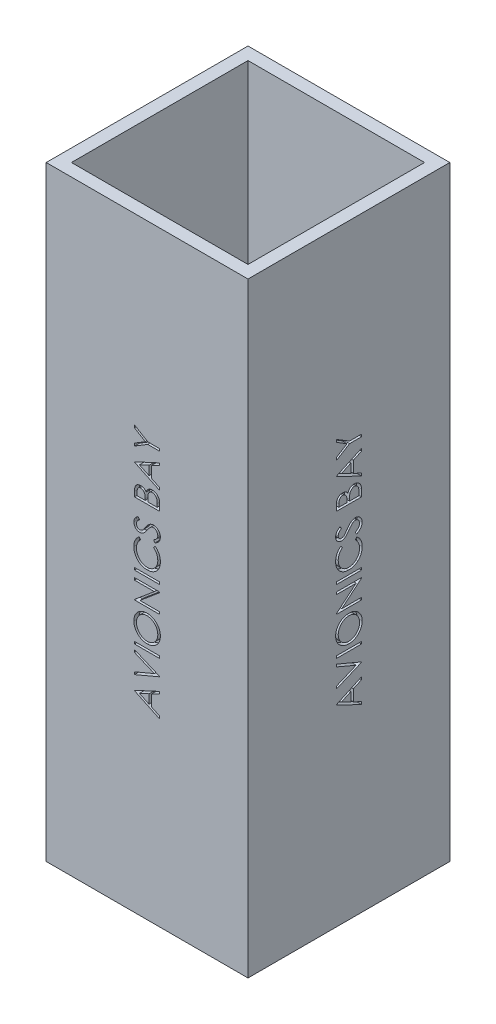
SolidWorks part; units mm, degrees
material "PVC Rigid"
ref_plane "Front Plane" through (0, 0, 0) normal (0, 0, 1) x (1, 0, 0)
ref_plane "Top Plane" through (0, 0, 0) normal (0, 1, 0) x (1, 0, 0)
ref_plane "Right Plane" through (0, 0, 0) normal (1, 0, 0) x (0, 0, -1)
sketch "Sketch1" plane through (0, 0, 0) normal (0, 1, 0) x (1, 0, 0)
  line L1 (-50.8, -50.8) -> (50.8, -50.8)
  line L2 (-50.8, -50.8) -> (-50.8, 50.8)
  line L3 (-50.8, 50.8) -> (50.8, 50.8)
  line L4 (50.8, -50.8) -> (50.8, 50.8)
  line L5 (-50.8, -50.8) -> (50.8, 50.8) construction
  line L6 (-50.8, 50.8) -> (50.8, -50.8) construction
  line L7 (-44.45, -44.45) -> (44.45, -44.45)
  line L8 (-44.45, -44.45) -> (-44.45, 44.45)
  line L9 (-44.45, 44.45) -> (44.45, 44.45)
  line L10 (44.45, -44.45) -> (44.45, 44.45)
  line L11 (-44.45, -44.45) -> (44.45, 44.45) construction
  line L12 (-44.45, 44.45) -> (44.45, -44.45) construction
  point P0 (0, 0)
  point P6 (0, 0)
  dimension "D1" = 101.6
  dimension "D2" = 101.6
  dimension "D3" = 88.9
extrude "Boss-Extrude1" add sketch "Sketch1" along normal blind 304.8
sketch "Sketch6" plane through (-50.8, 0, 0) normal (-1, 0, 0) x (0, 0, 1)
  line L0 (6.35, 0) -> (6.35, 304.8) construction
  line L1 (-50.8, 0) -> (50.8, 0) construction
  line L2 (-50.8, 304.8) -> (50.8, 304.8) construction
  line L3 (-50.8, 304.8) -> (-50.8, 0) construction
  text T0 "AVIONICS BAY" font "Century Gothic" height in points 48
  dimension "D1" = 57.15
extrude "Cut-Extrude1" cut sketch "Sketch6" against normal blind 2.54
sketch "Sketch7" plane through (0, 0, 0) normal (0, 0, 1) x (1, 0, 0)
  line L0 (0, 0) -> (0, 304.8) construction
  line L1 (-50.8, 304.8) -> (50.8, 304.8) construction
pattern_circular "CirPattern1" count 4 over 360 about axis through (0, 0, 0) along (0, 1, 0) of "Cut-Extrude1"
